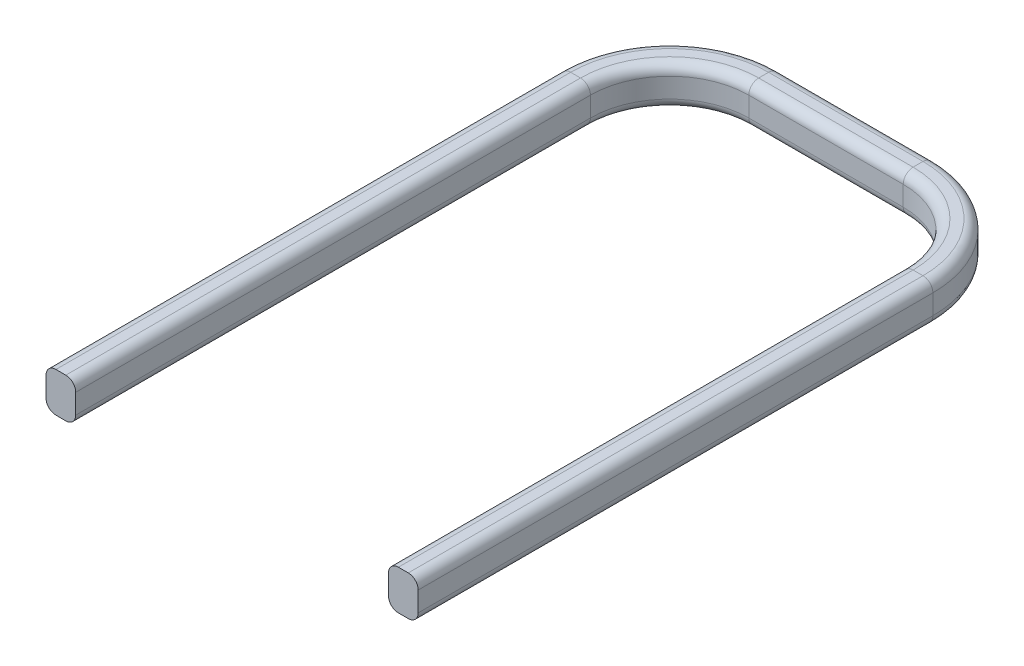
SolidWorks part; units mm, degrees
material "Cast Alloy Steel"
ref_plane "Front Plane" through (0, 0, 0) normal (0, 0, 1) x (1, 0, 0)
ref_plane "Top Plane" through (0, 0, 0) normal (0, 1, 0) x (1, 0, 0)
ref_plane "Right Plane" through (0, 0, 0) normal (1, 0, 0) x (0, 0, -1)
sketch "Sketch1" plane through (0, 0, 0) normal (0, 1, 0) x (1, 0, 0)
  line L0 (-3.95, 0) -> (-3.95, 13)
  line L1 (-1.95, 15) -> (1.95, 15)
  line L2 (3.95, 13) -> (3.95, 0)
  arc A0 (1.95, 15) -> (3.95, 13) centre (1.95, 13) cw
  arc A1 (-3.95, 13) -> (-1.95, 15) centre (-1.95, 13) cw
  point P6 (0, 15)
  point P11 (-3.95, 15)
  dimension "D3" = 2
  dimension "D1" = 3.95
  dimension "D2" = 15
sketch "Sketch2" plane through (0, 0, 0) normal (0, 0, 1) x (1, 0, 0)
  line L1 (3.95, 0) -> (4.7, 0)
  line L2 (3.95, 0) -> (3.95, 1)
  line L3 (3.95, 1) -> (4.7, 1)
  line L4 (4.7, 0) -> (4.7, 1)
  dimension "D1" = 1
  dimension "D2" = 0.75
sweep "Sweep1" add profiles "Sketch2" path "Sketch1"
fillet "Fillet1" radius 0.25 20 edges at (3.95, 1, -6.5) (3.3642, 1, -14.4142) (0, 1, -15) (-3.3642, 1, -14.4142) (-4.7, 1, -6.5) (-3.8945, 1, -14.9445) (0, 1, -15.75) (3.8945, 1, -14.9445) (-3.95, 0, -6.5) (-3.3642, 0, -14.4142) (0, 0, -15) (3.3642, 0, -14.4142) (-4.7, 0, -6.5) (-3.8945, 0, -14.9445) (0, 0, -15.75) (3.8945, 0, -14.9445) (-3.95, 1, -6.5) (4.7, 1, -6.5) (3.95, 0, -6.5) (4.7, 0, -6.5)
